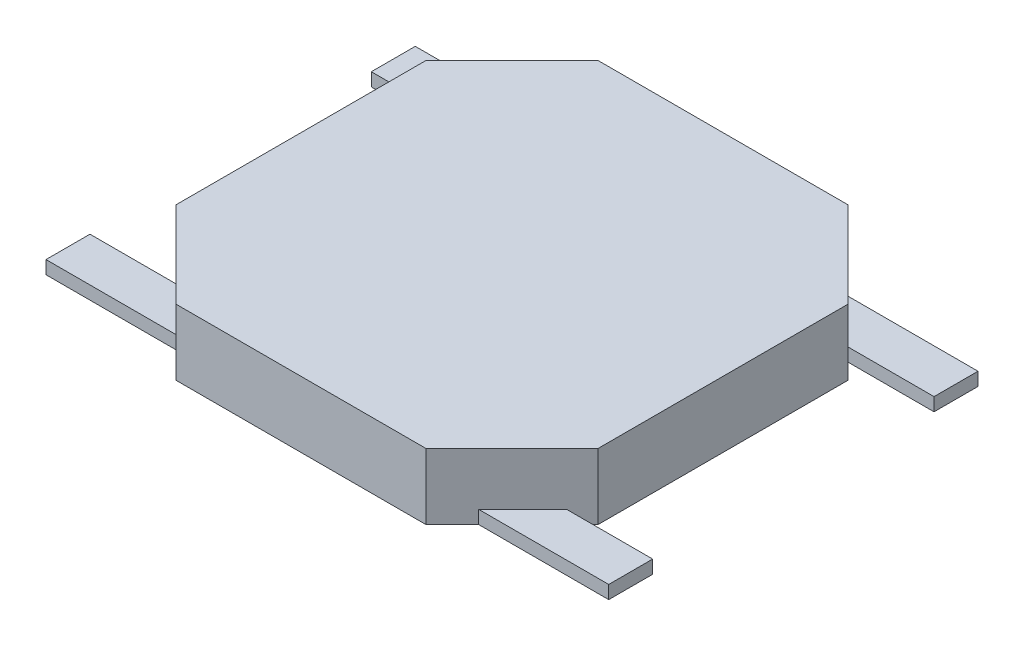
SolidWorks part; units mm, degrees
ref_plane "前视基准面" through (0, 0, 0) normal (0, 0, 1) x (1, 0, 0)
ref_plane "上视基准面" through (0, 0, 0) normal (0, 1, 0) x (1, 0, 0)
ref_plane "右视基准面" through (0, 0, 0) normal (1, 0, 0) x (0, 0, -1)
sketch "草图1" plane through (0, 0, 0) normal (0, 1, 0) x (1, 0, 0)
  line L0 (-1.42, 2.4) -> (1.42, 2.4)
  line L5 (1.42, 2.4) -> (2.4, 1.42)
  line L6 (2.4, 1.42) -> (2.4, -1.42)
  line L7 (2.4, -1.42) -> (1.42, -2.4)
  line L8 (1.42, -2.4) -> (-1.42, -2.4)
  line L9 (-1.42, -2.4) -> (-2.4, -1.42)
  line L10 (-2.4, -1.42) -> (-2.4, 1.42)
  line L11 (-2.4, 1.42) -> (-1.42, 2.4)
  point P0 (2.337, 1.4185)
  point P9 (0, 2.4)
  point P11 (2.4, 0)
  point P15 (0, -2.4)
  point P19 (-2.4, 0)
  point P20 (0, 0)
  dimension "D1" = 4
  dimension "D2" = 4.8
  dimension "D3" = 2.84
extrude "凸台-拉伸1" add sketch "草图1" along normal blind 0.75
sketch "草图2" plane through (0, 0, 0) normal (0, -1, 0) x (1, 0, 0)
  line L0 (3.2, 1.6) -> (-3.2, 1.6)
  line L1 (-3.2, -1.6) -> (3.2, -1.6)
  line L2 (-3.2, -1.6) -> (-3.2, -2.1)
  line L3 (-3.2, -2.1) -> (3.2, -2.1)
  line L4 (3.2, -1.6) -> (3.2, -2.1)
  line L5 (-3.2, -1.6) -> (3.2, -2.1) construction
  line L6 (-3.2, -2.1) -> (3.2, -1.6) construction
  line L7 (3.2, 1.6) -> (3.2, 2.1)
  line L8 (3.2, 2.1) -> (-3.2, 2.1)
  line L9 (-3.2, 1.6) -> (-3.2, 2.1)
  line L10 (3.2, 1.6) -> (-3.2, 2.1) construction
  line L11 (3.2, 2.1) -> (-3.2, 1.6) construction
  point P0 (0, -1.85)
  point P5 (0, 0)
  point P6 (0, 0)
  point P7 (0, 1.85)
  point P13 (0, 0)
  dimension "D1" = 0.5
  dimension "D2" = 6.4
  dimension "D4" = 3.7
  dimension "D3" = 2
extrude "凸台-拉伸2" add sketch "草图2" against normal blind 0.15
